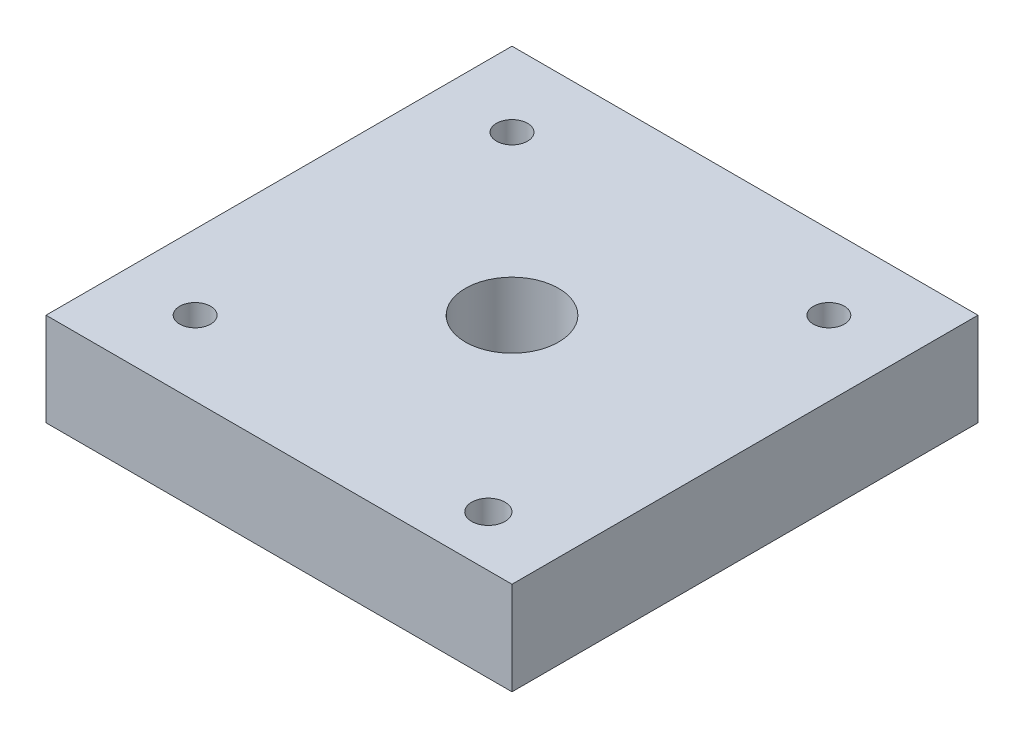
SolidWorks part; units mm, degrees
ref_plane "Front Plane" through (0, 0, 0) normal (0, 0, 1) x (1, 0, 0)
ref_plane "Top Plane" through (0, 0, 0) normal (0, 1, 0) x (1, 0, 0)
ref_plane "Right Plane" through (0, 0, 0) normal (1, 0, 0) x (0, 0, -1)
sketch "Sketch1" plane through (0, 0, 0) normal (0, 1, 0) x (1, 0, 0)
  line L1 (-25, -25) -> (25, -25)
  line L2 (-25, -25) -> (-25, 25)
  line L3 (-25, 25) -> (25, 25)
  line L4 (25, -25) -> (25, 25)
  line L5 (-25, -25) -> (25, 25) construction
  line L6 (-25, 25) -> (25, -25) construction
  circle A0 centre (0, 0) radius 5
  circle A1 centre (-17, 17) radius 1.666
  circle A2 centre (17, 17) radius 1.666
  circle A3 centre (-17, -17) radius 1.666
  circle A4 centre (17, -19.537) radius 1.7939
  dimension "D1" = 50
  dimension "D3" = 8
  dimension "D2" = 50
  dimension "D4" = 8
  dimension "D5" = 8
  dimension "D6" = 8
  dimension "D7" = 8
  dimension "D8" = 8
  dimension "D9" = 8
  dimension "D10" = 8
extrude "Boss-Extrude3" add sketch "Sketch1" along normal blind 10
